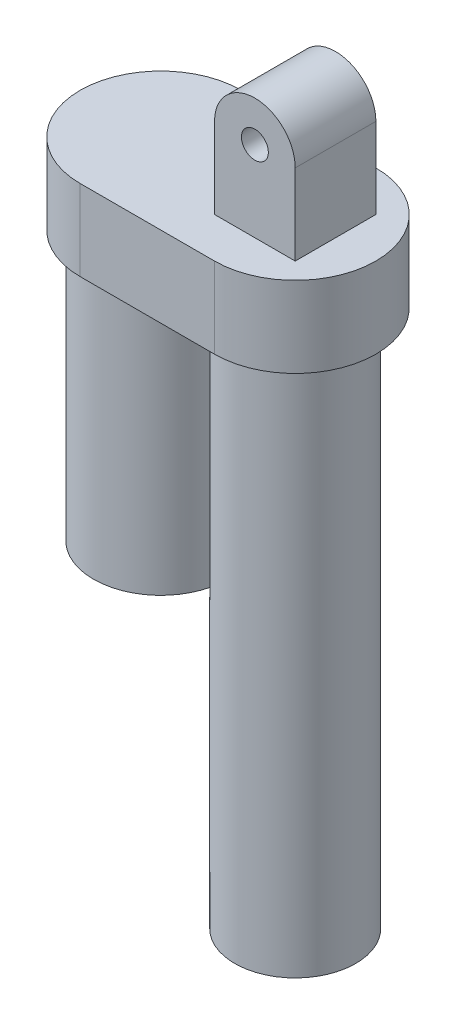
SolidWorks part; units mm, degrees
ref_plane "Plano frontal" through (0, 0, 0) normal (0, 0, 1) x (1, 0, 0)
ref_plane "Plano superior" through (0, 0, 0) normal (0, 1, 0) x (1, 0, 0)
ref_plane "Plano direito" through (0, 0, 0) normal (1, 0, 0) x (0, 0, -1)
sketch "Esboço1" plane through (0, 0, 0) normal (0, 0, 1) x (1, 0, 0)
  line L0 (0, 0) -> (0, 389.2229) construction
  line L1 (0, 0) -> (207.2703, 0) construction
  line L2 (9, 200) -> (22.5, 200)
  line L3 (22.5, 200) -> (22.5, 0)
  line L4 (9, 0) -> (22.5, 0)
  line L6 (9, 200) -> (9, 0)
  dimension "D1" = 45
  dimension "D2" = 200
  dimension "D3" = 18
revolve "Revolução1" add sketch "Esboço1" angle 360 about L0
sketch "Esboço2" plane through (0, 200, 0) normal (0, 1, 0) x (1, 0, 0)
  line L0 (0, 0) -> (-50, 0) construction
  line L1 (0, -30) -> (-50, -30)
  line L2 (0, 30) -> (-50, 30)
  arc A0 (0, -30) -> (0, 30) centre (0, 0) ccw
  arc A1 (-50, 30) -> (-50, -30) centre (-50, 0) ccw
  point P3 (-25, 0)
  dimension "D1" = 30
  dimension "D2" = 50
extrude "Ressalto-extrusão1" add sketch "Esboço2" along normal blind 30
sketch "Esboço3" plane through (0, 0, 0) normal (0, 0, 1) x (1, 0, 0)
  line L0 (-50, 200) -> (-50, 0) construction
  line L1 (-50, 200) -> (-25, 200)
  line L2 (-50, 200) -> (0, 200) construction
  line L3 (-25, 200) -> (-25, 100)
  line L4 (-25, 100) -> (-50, 100)
  line L5 (-50, 100) -> (-50, 200)
  dimension "D1" = 50
  dimension "D2" = 100
revolve "Revolução2" add sketch "Esboço3" angle 360 about L0
sketch "Esboço4" plane through (0, 0, 0) normal (0, 0, 1) x (1, 0, 0)
  line L0 (0, 230) -> (0, 329.8851) construction
  line L1 (15, 230) -> (15, 260)
  line L2 (30, 230) -> (0, 230) construction
  line L3 (-15, 230) -> (-15, 260)
  line L4 (15, 230) -> (-15, 230)
  arc A0 (15, 260) -> (-15, 260) centre (0, 260) ccw
  circle A1 centre (0, 260) radius 5
  dimension "D3" = 10
  dimension "D1" = 30
  dimension "D2" = 30
extrude "Ressalto-extrusão2" add sketch "Esboço4" along normal mid plane 30
